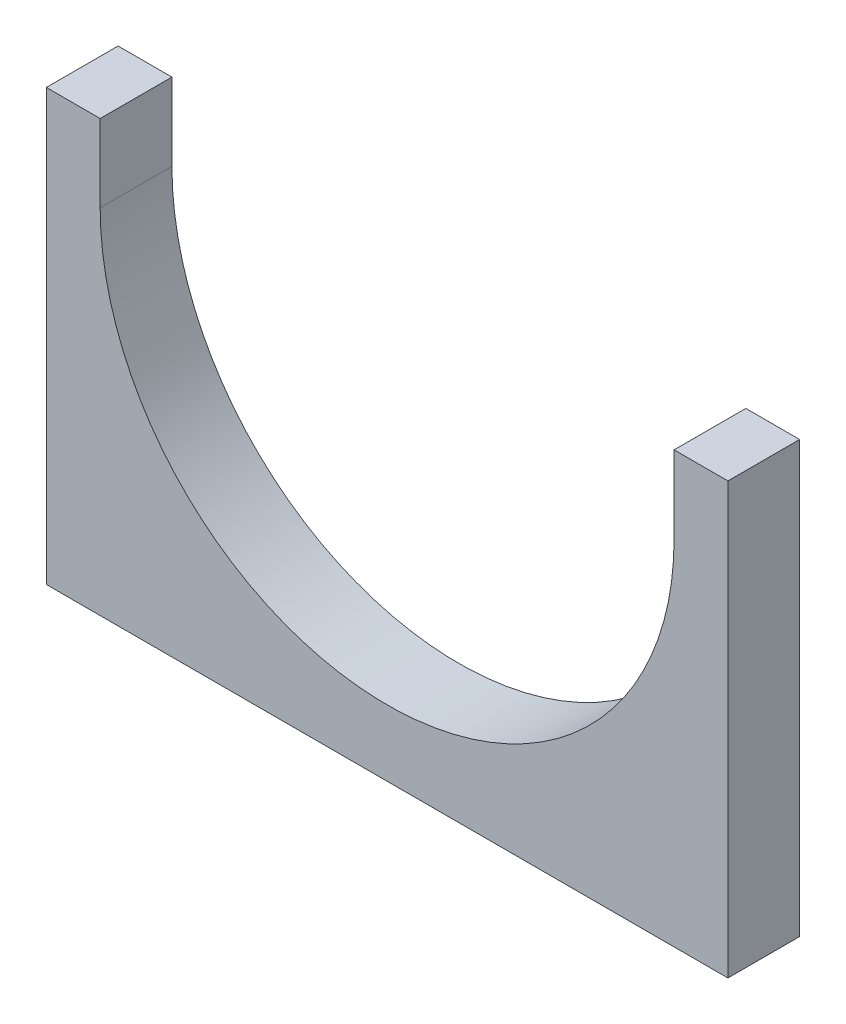
SolidWorks part; units mm, degrees
ref_plane "Front Plane" through (0, 0, 0) normal (0, 0, 1) x (1, 0, 0)
ref_plane "Top Plane" through (0, 0, 0) normal (0, 1, 0) x (1, 0, 0)
ref_plane "Right Plane" through (0, 0, 0) normal (1, 0, 0) x (0, 0, -1)
sketch "Sketch1" plane through (0, 0, 0) normal (0, 0, 1) x (1, 0, 0)
  line L0 (76.2, 500) -> (76.2, 609.6)
  line L1 (0, 0) -> (965.1, 0)
  line L2 (0, 0) -> (0, 609.6)
  line L3 (0, 609.6) -> (76.2, 609.6)
  line L4 (965.1, 0) -> (965.1, 609.6)
  line L5 (888.9, 609.6) -> (965.1, 609.6)
  line L6 (888.9, 500) -> (888.9, 609.6)
  arc A0 (76.2, 500) -> (888.9, 500) centre (482.55, 500) ccw
extrude "Boss-Extrude1" add sketch "Sketch1" along normal blind 101.6
